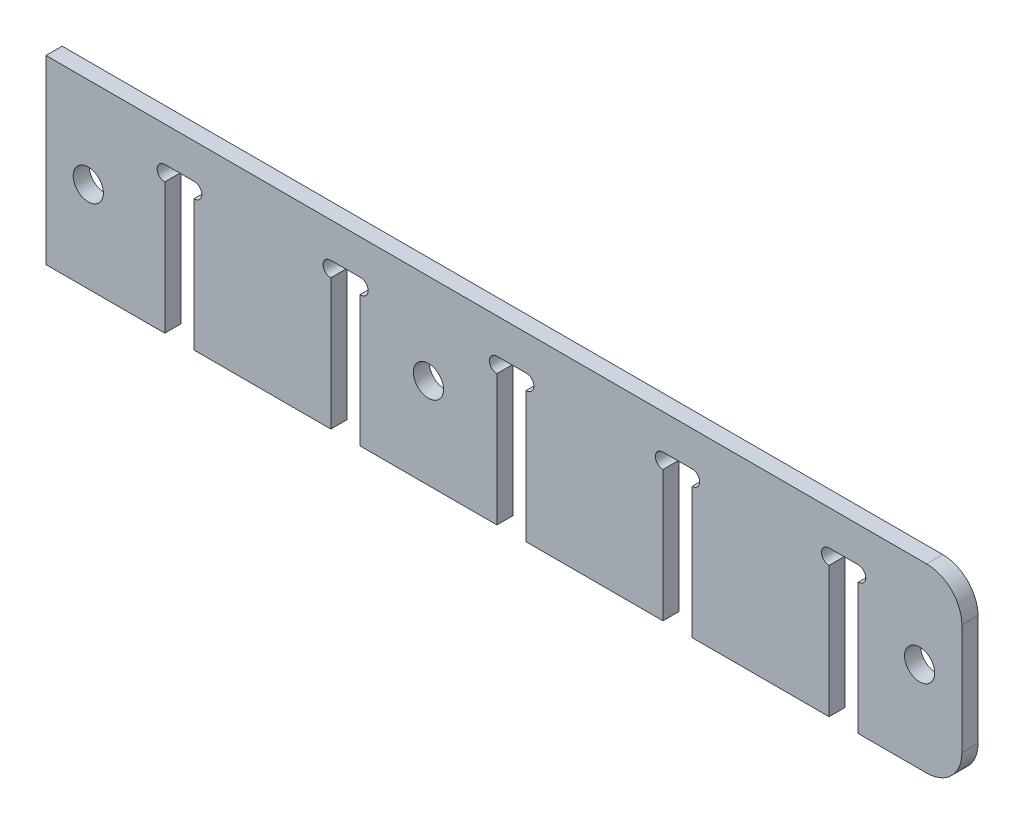
SolidWorks part; units mm, degrees
material "Mosiądz"
ref_plane "Płaszczyzna przednia" through (0, 0, 0) normal (0, 0, 1) x (1, 0, 0)
ref_plane "Płaszczyzna górna" through (0, 0, 0) normal (0, 1, 0) x (1, 0, 0)
ref_plane "Płaszczyzna prawa" through (0, 0, 0) normal (1, 0, 0) x (0, 0, -1)
sketch "Szkic1" plane through (0, 0, 0) normal (0, 0, 1) x (1, 0, 0)
  line L1 (-30.5057, 25.9815) -> (60.4943, 25.9815)
  line L2 (-30.5057, 25.9815) -> (-30.5057, 7.9815)
  line L3 (-30.5057, 7.9815) -> (60.4943, 7.9815)
  line L4 (60.4943, 25.9815) -> (60.4943, 7.9815)
  dimension "D1" = 91
  dimension "D2" = 18
extrude "Dodanie-wyciągnięcie1" add sketch "Szkic1" along normal blind 1.6
sketch "Szkic2" plane through (0, 0, 1.6) normal (0, 0, 1) x (1, 0, 0)
  line L0 (14.9943, 25.9815) -> (14.9943, 7.9815) construction
  line L1 (60.4943, 25.9815) -> (-30.5057, 25.9815) construction
  line L2 (-30.5057, 7.9815) -> (60.4943, 7.9815) construction
sketch "Szkic3" plane through (0, 0, 0) normal (0, 0, -1) x (-1, 0, 0)
  line L0 (-14.9943, 25.9815) -> (-14.9943, 7.9815) construction
  line L1 (-60.4943, 25.9815) -> (30.5057, 25.9815) construction
  line L2 (30.5057, 7.9815) -> (-60.4943, 7.9815) construction
ref_plane "Płaszczyzna1" through (14.9943, 0, 0) normal (1, 0, 0) x (0, 0, -1)
fillet "Zaokrąglenie2" radius 3.5 2 edges at (60.4943, 7.9815, 0.8) (60.4943, 25.9815, 0.8)
sketch "Szkic5" plane through (0, 0, 1.6) normal (0, 0, 1) x (1, 0, 0)
  line L1 (-18.7057, 7.9815) -> (-18.7057, 22.5015)
  line L2 (-18.7057, 7.9815) -> (-15.8057, 7.9815)
  line L5 (-15.8057, 7.9815) -> (-15.8057, 22.5015)
  line L7 (-18.7057, 22.5015) -> (-15.8057, 22.5015)
  line L9 (-2.2057, 7.9815) -> (-2.2057, 22.5015)
  line L10 (-2.2057, 7.9815) -> (0.6943, 7.9815)
  line L11 (0.6943, 7.9815) -> (0.6943, 22.5015)
  line L12 (-2.2057, 22.5015) -> (0.6943, 22.5015)
  line L13 (14.2943, 7.9815) -> (14.2943, 22.5015)
  line L14 (14.2943, 7.9815) -> (17.1943, 7.9815)
  line L15 (17.1943, 7.9815) -> (17.1943, 22.5015)
  line L16 (14.2943, 22.5015) -> (17.1943, 22.5015)
  line L17 (30.7943, 7.9815) -> (30.7943, 22.5015)
  line L18 (30.7943, 7.9815) -> (33.6943, 7.9815)
  line L19 (33.6943, 7.9815) -> (33.6943, 22.5015)
  line L20 (30.7943, 22.5015) -> (33.6943, 22.5015)
  line L21 (47.2943, 7.9815) -> (47.2943, 22.5015)
  line L22 (47.2943, 7.9815) -> (50.1943, 7.9815)
  line L23 (50.1943, 7.9815) -> (50.1943, 22.5015)
  line L24 (47.2943, 22.5015) -> (50.1943, 22.5015)
  dimension "D1" = 5
extrude "Wytnij-wyciągnięcie2" cut sketch "Szkic5" against normal up to surface (1.6 mm away) up to face at (29.2359, 16.9815, 0)
sketch "Szkic7" plane through (0, 0, 1.6) normal (0, 0, 1) x (1, 0, 0)
  line L0 (56.9943, 25.9815) -> (-30.5057, 25.9815) construction
  line L1 (14.9943, -21.338) -> (14.9943, 21.338) construction
  circle A0 centre (-26.3057, 16.9815) radius 1.5
  circle A1 centre (56.2943, 16.9815) radius 1.5
  dimension "D1" = 3
  dimension "D4" = 3
  dimension "D2" = 9
  dimension "D3" = 41.3
  dimension "D5" = 9
  dimension "D6" = 41.3
extrude "Wytnij-wyciągnięcie3" cut sketch "Szkic7" against normal up to surface (1.6 mm away) up to face at (18.8578, 15.6431, 0)
sketch "Szkic8" plane through (0, 0, 1.6) normal (0, 0, 1) x (1, 0, 0)
  line L0 (-46.0941, 16.9815) -> (-14.9172, 16.9815) construction
sketch "Szkic9" plane through (0, 0, 0) normal (0, 0, -1) x (-1, 0, 0)
  line L0 (46.0941, 16.9815) -> (14.9172, 16.9815) construction
ref_plane "Płaszczyzna2" through (0, 16.9815, 0) normal (0, 1, 0) x (1, 0, 0)
sketch "Szkic10" plane through (0, 0, 1.6) normal (0, 0, 1) x (1, 0, 0)
  line L0 (-26.3057, 16.9815) -> (56.2943, 16.9815) construction
  line L1 (7.4943, 7.9815) -> (7.4943, 32.7506) construction
  line L2 (0.6943, 7.9815) -> (14.2943, 7.9815) construction
  circle A0 centre (7.4943, 16.9815) radius 1.5
extrude "Wytnij-wyciągnięcie4" cut sketch "Szkic10" against normal up to surface (1.6 mm away) up to face at (57.7943, 16.9815, 0)
sketch "Szkic11" plane through (0, 0, 0) normal (0, 0, -1) x (-1, 0, 0)
  line L0 (-55.0206, 21.7515) -> (28.5711, 21.7515) construction
  line L1 (18.7057, 22.5015) -> (15.8057, 22.5015) construction
  line L2 (18.7057, 7.9815) -> (18.7057, 22.5015) construction
  line L3 (-14.2943, 7.9815) -> (-14.2943, 22.5015) construction
  line L4 (-33.6943, 22.5015) -> (-33.6943, 7.9815) construction
  line L5 (-47.2943, 7.9815) -> (-47.2943, 22.5015) construction
  line L6 (-50.1943, 22.5015) -> (-50.1943, 7.9815) construction
  circle A0 centre (18.7057, 21.7515) radius 0.75
  circle A1 centre (15.7735, 21.7515) radius 0.75
  circle A2 centre (2.227, 21.7515) radius 0.7503
  circle A3 centre (-0.7501, 21.7515) radius 0.7521
  circle A4 centre (-14.2943, 21.7515) radius 0.75
  circle A5 centre (-17.217, 21.7515) radius 0.7503
  circle A6 centre (-30.7888, 21.7515) radius 0.75
  circle A7 centre (-33.6943, 21.7515) radius 0.75
  circle A8 centre (-47.2943, 21.7515) radius 0.75
  circle A9 centre (-50.1943, 21.7515) radius 0.75
  dimension "D1" = 0.75
extrude "Wytnij-wyciągnięcie5" cut sketch "Szkic11" against normal up to surface (1.6 mm away) up to face at (8.9943, 16.9815, 1.6)
